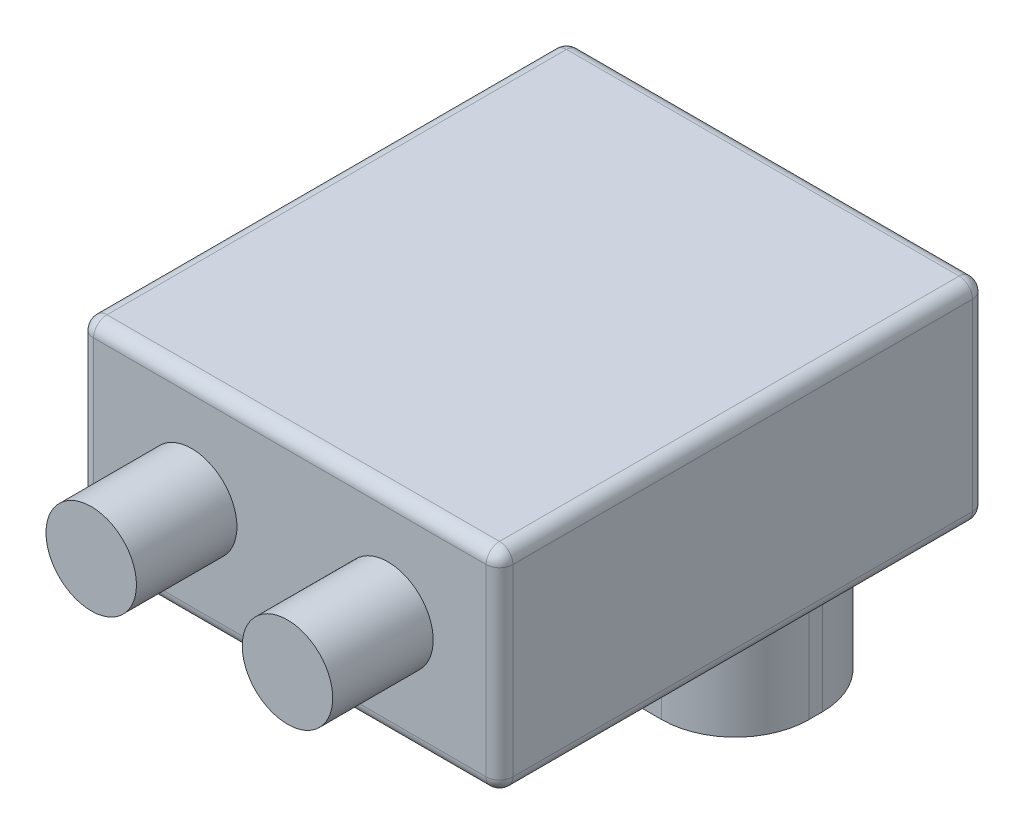
SolidWorks part; units mm, degrees
material "ABS"
ref_plane "X-Y Datum" through (0, 0, 0) normal (0, 0, 1) x (1, 0, 0)
ref_plane "X-Z Datum" through (0, 0, 0) normal (0, 1, 0) x (1, 0, 0)
ref_plane "Y-Z Datum" through (0, 0, 0) normal (1, 0, 0) x (0, 0, -1)
sketch "Sketch1" plane through (0, 0, 0) normal (0, 1, 0) x (1, 0, 0)
  line L1 (-31.3, 36.3) -> (31.3, 36.3)
  line L2 (-31.3, 36.3) -> (-31.3, -36.3)
  line L3 (-31.3, -36.3) -> (31.3, -36.3)
  line L4 (31.3, 36.3) -> (31.3, -36.3)
  line L5 (-31.3, 36.3) -> (31.3, -36.3) construction
  line L6 (-31.3, -36.3) -> (31.3, 36.3) construction
  point P0 (0, 0)
  dimension "D1" = 62.6
  dimension "D2" = 72.6
extrude "Boss-Extrude1" add sketch "Sketch1" along normal blind 24.14
sketch "Sketch2" plane through (0, 0, 0) normal (0, -1, 0) x (1, 0, 0)
  line L0 (25, -17.2) -> (-25, -17.2) construction
  line L6 (-25, -5.2) -> (25, -5.2)
  line L7 (-25, -5.2) -> (-25, -29.2)
  line L8 (-25, -29.2) -> (25, -29.2)
  line L9 (25, -5.2) -> (25, -29.2)
  line L11 (-31.3, 36.3) -> (31.3, 36.3) construction
  point P4 (0, -17.2)
  dimension "D1" = 65.5
  dimension "D2" = 24
  dimension "D3" = 50
extrude "Boss-Extrude2" add sketch "Sketch2" along normal blind 19
sketch "Sketch3" plane through (0, 24.14, 0) normal (0, 1, 0) x (1, 0, 0)
  line L4 (31.3, -36.3) -> (31.3, 36.3)
  line L5 (31.3, 36.3) -> (-31.3, 36.3)
  line L6 (-31.3, 36.3) -> (-31.3, -36.3)
  line L7 (-31.3, -36.3) -> (31.3, -36.3)
  line L8 (31.3, -36.3) -> (31.3, 36.3)
  line L9 (31.3, 36.3) -> (-31.3, 36.3)
  line L10 (-31.3, 36.3) -> (-31.3, -36.3)
  line L11 (-31.3, -36.3) -> (31.3, -36.3)
  dimension "D1" = 0
extrude "Boss-Extrude3" add sketch "Sketch3" along normal blind 7.3
fillet "Fillet1" radius 2 12 edges at (0, 0, -36.3) (0, 0, 36.3) (-31.3, 15.72, -36.3) (-31.3, 15.72, 36.3) (-31.3, 0, 0) (31.3, 15.72, 36.3) (31.3, 15.72, -36.3) (31.3, 0, 0) (0, 31.44, -36.3) (0, 31.44, 36.3) (-31.3, 31.44, 0) (31.3, 31.44, 0)
fillet "Fillet2" radius 11 4 edges at (25, -9.5, -5.2) (25, -9.5, -29.2) (-25, -9.5, -29.2) (-25, -9.5, -5.2)
sketch "Sketch4" plane through (0, 0, 36.3) normal (0, 0, 1) x (1, 0, 0)
  line L0 (0, 0) -> (0, 29.44) construction
  line L1 (29.3, 29.44) -> (-29.3, 29.44) construction
  line L2 (-29.3, 2) -> (29.3, 2) construction
  circle A0 centre (-14.65, 15.72) radius 6.75
  circle A2 centre (14.65, 15.72) radius 6.75
  dimension "D1" = 13.5
  dimension "D2" = 13.72
  dimension "D3" = 14.65
extrude "Boss-Extrude4" add sketch "Sketch4" along normal blind 15
